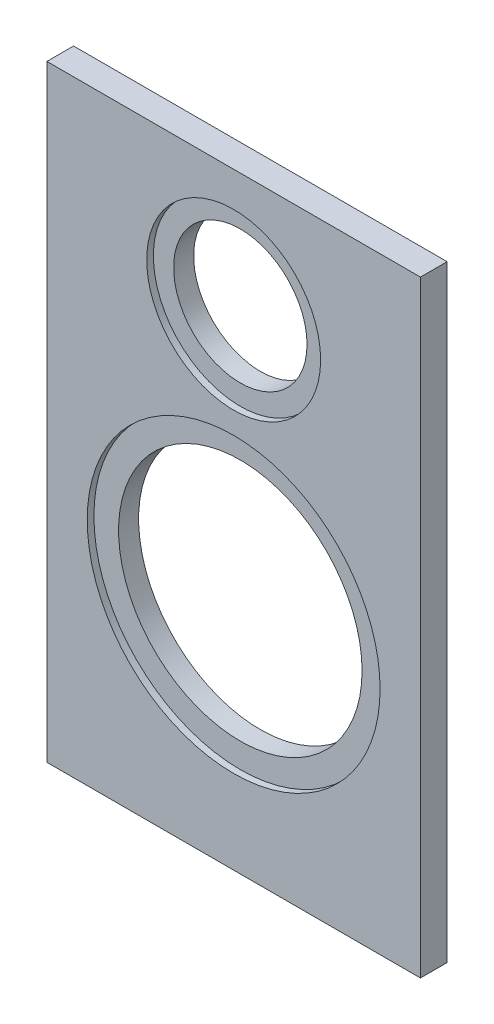
SolidWorks part; units mm, degrees
material "Mahogany"
ref_plane "Front Plane" through (0, 0, 0) normal (0, 0, 1) x (1, 0, 0)
ref_plane "Top Plane" through (0, 0, 0) normal (0, 1, 0) x (1, 0, 0)
ref_plane "Right Plane" through (0, 0, 0) normal (1, 0, 0) x (0, 0, -1)
sketch "Sketch1" plane through (0, 0, 0) normal (0, 0, 1) x (1, 0, 0)
  line L1 (112, -182) -> (-112, -182)
  line L2 (112, -182) -> (112, 182)
  line L3 (112, 182) -> (-112, 182)
  line L4 (-112, -182) -> (-112, 182)
  line L5 (112, -182) -> (-112, 182) construction
  line L6 (112, 182) -> (-112, -182) construction
  point P0 (0, 0)
  dimension "D1" = 224
  dimension "D2" = 364
extrude "Boss-Extrude1" add sketch "Sketch1" along normal blind 16
sketch "Sketch2" plane through (0, 0, 16) normal (0, 0, 1) x (1, 0, 0)
  line L0 (0, 182) -> (0, -182) construction
  line L1 (112, 182) -> (-112, 182) construction
  line L2 (-112, -182) -> (112, -182) construction
  circle A0 centre (0, 109) radius 52.15
  circle A1 centre (0, -44) radius 87.8
  dimension "D3" = 104.3
  dimension "D4" = 175.6
  dimension "D1" = 73
  dimension "D2" = 226
extrude "Cut-Extrude1" cut sketch "Sketch2" against normal blind 4
sketch "Sketch3" plane through (0, 0, 16) normal (0, 0, 1) x (1, 0, 0)
  circle A0 centre (0, 109) radius 40
  circle A1 centre (0, -44) radius 73
  dimension "D1" = 80
  dimension "D2" = 146
extrude "Cut-Extrude2" cut sketch "Sketch3" against normal through all
